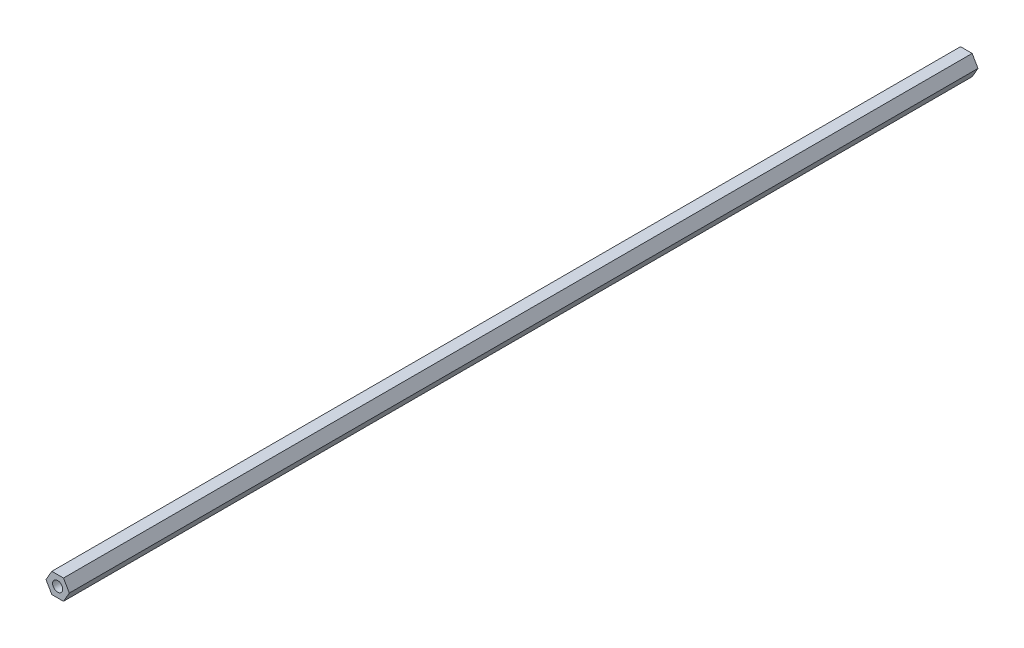
SolidWorks part; units mm, degrees
ref_plane "Front Plane" through (0, 0, 0) normal (0, 0, 1) x (1, 0, 0)
ref_plane "Top Plane" through (0, 0, 0) normal (0, 1, 0) x (1, 0, 0)
ref_plane "Right Plane" through (0, 0, 0) normal (1, 0, 0) x (0, 0, -1)
sketch "Sketch1" plane through (0, 0, 0) normal (0, 0, 1) x (1, 0, 0)
  line L0 (0, 6.35) -> (0, 0)
  line L1 (-7.3323, 0) -> (-3.6662, -6.35)
  line L2 (-3.6662, -6.35) -> (3.6662, -6.35)
  line L3 (3.6662, -6.35) -> (7.3323, 0)
  line L4 (7.3323, 0) -> (3.6662, 6.35)
  line L5 (3.6662, 6.35) -> (-3.6662, 6.35)
  line L6 (-3.6662, 6.35) -> (-7.3323, 0)
  circle A0 centre (0, 0) radius 6.35 construction
  dimension "D1" = 6.35
extrude "Boss-Extrude1" add sketch "Sketch1" along normal offset from surface (514.4834 mm away) 25.4
sketch "Sketch2" plane through (0, 0, 514.4834) normal (0, 0, 1) x (1, 0, 0)
  circle A0 centre (0, 0) radius 3.175
  dimension "D1" = 6.35
extrude "Cut-Extrude1" cut sketch "Sketch2" against normal through all both and the other way through all contours A0
sketch "Sketch3" plane through (0, 0, 514.4834) normal (0, 0, 1) x (1, 0, 0)
  line L1 (-3.6662, -6.35) -> (3.6662, -6.35)
  line L2 (3.6662, -6.35) -> (7.3323, 0)
  line L3 (7.3323, 0) -> (3.6662, 6.35)
  line L4 (3.6662, 6.35) -> (-3.6662, 6.35)
  line L5 (-3.6662, 6.35) -> (-7.3323, 0)
  line L6 (-7.3323, 0) -> (-3.6662, -6.35)
  circle A0 centre (0, 0) radius 6.35 construction
  circle A1 centre (0, 0) radius 3.175
extrude "Boss-Extrude2" add sketch "Sketch3" against normal blind 571.5
